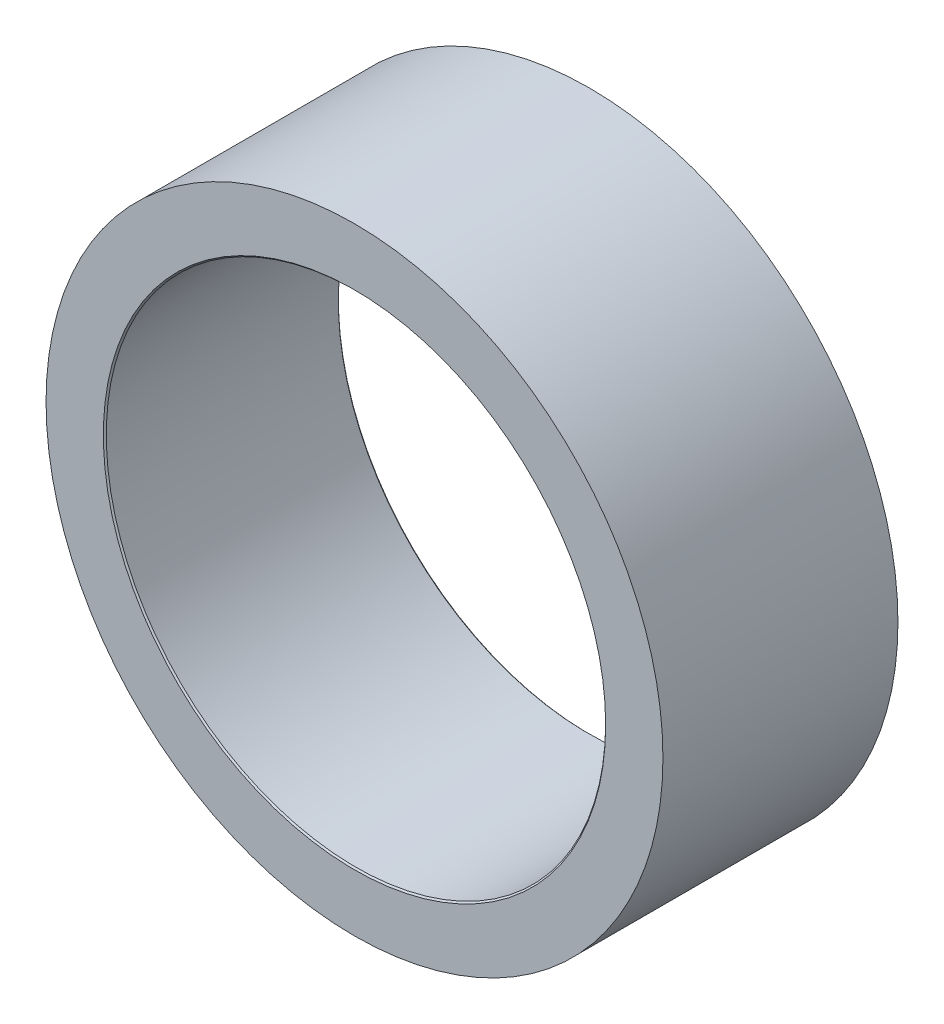
SolidWorks part; units mm, degrees
ref_plane "Front Plane" through (0, 0, 0) normal (0, 0, 1) x (1, 0, 0)
ref_plane "Top Plane" through (0, 0, 0) normal (0, 1, 0) x (1, 0, 0)
ref_plane "Right Plane" through (0, 0, 0) normal (1, 0, 0) x (0, 0, -1)
sketch "Sketch2" plane through (0, 0, 0) normal (0, 0, 1) x (1, 0, 0)
  circle A0 centre (0, 0) radius 10.5
extrude "Boss-Extrude1" add sketch "Sketch2" against normal blind 8
sketch "Sketch3" plane through (0, 0, 0) normal (0, 0, 1) x (1, 0, 0)
  circle A0 centre (0, 0) radius 8.5
extrude "Cut-Extrude1" cut sketch "Sketch3" against normal through all
chamfer "Chamfer1" distance 0.05 angle 45 1 edges at (8.5, 0, 0)
chamfer "Chamfer2" distance 0.05 angle 45 1 edges at (8.5, 0, -8)
